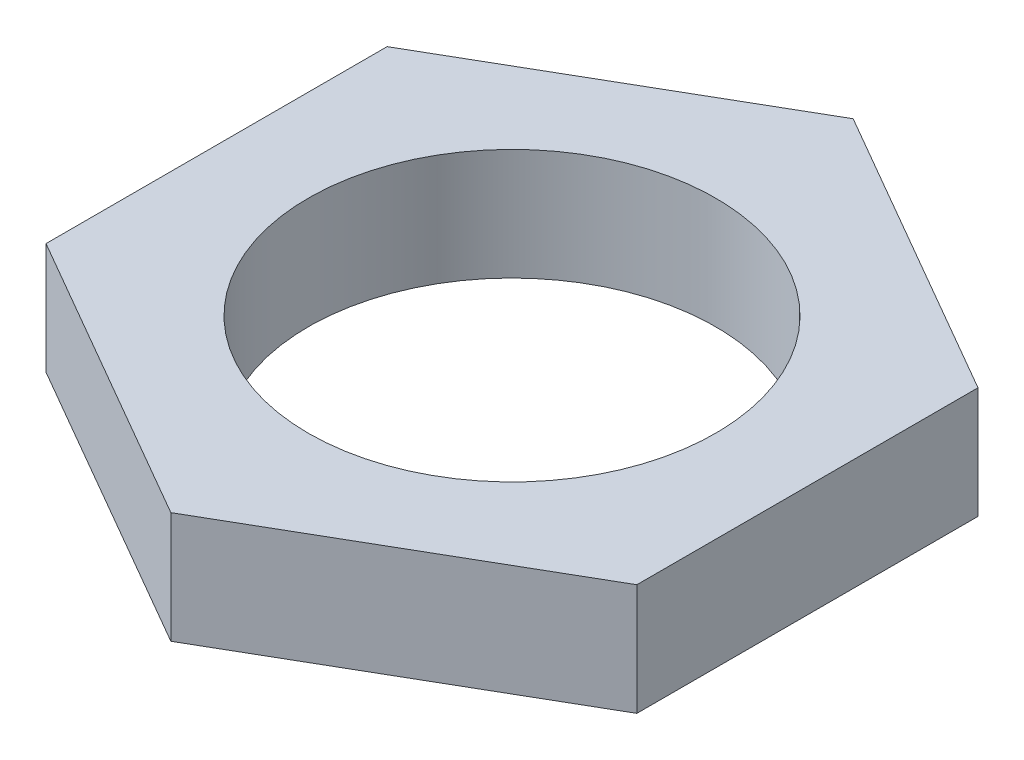
SolidWorks part; units mm, degrees
ref_plane "Front" through (0, 0, 0) normal (0, 0, 1) x (1, 0, 0)
ref_plane "Top" through (0, 0, 0) normal (0, 1, 0) x (1, 0, 0)
ref_plane "Right" through (0, 0, 0) normal (1, 0, 0) x (0, 0, -1)
sketch "Sketch1" plane through (0, 0, 0) normal (0, 1, 0) x (1, 0, 0)
  line L1 (-3.5, 2.0207) -> (-3.5, -2.0207)
  line L2 (-3.5, -2.0207) -> (0, -4.0415)
  line L3 (0, -4.0415) -> (3.5, -2.0207)
  line L4 (3.5, -2.0207) -> (3.5, 2.0207)
  line L5 (3.5, 2.0207) -> (0, 4.0415)
  line L6 (0, 4.0415) -> (-3.5, 2.0207)
  circle A0 centre (0, 0) radius 3.5 construction
  dimension "D1" = 7
  dimension "D2" = 8.0829
extrude "Boss-Extrude1" add sketch "Sketch1" along normal blind 1.32
sketch "Sketch2" plane through (0, 1.32, 0) normal (0, 1, 0) x (1, 0, 0)
  circle A0 centre (0, 0) radius 2.413
  dimension "D1" = 4.826
extrude "Cut-Extrude1" cut sketch "Sketch2" against normal through all
